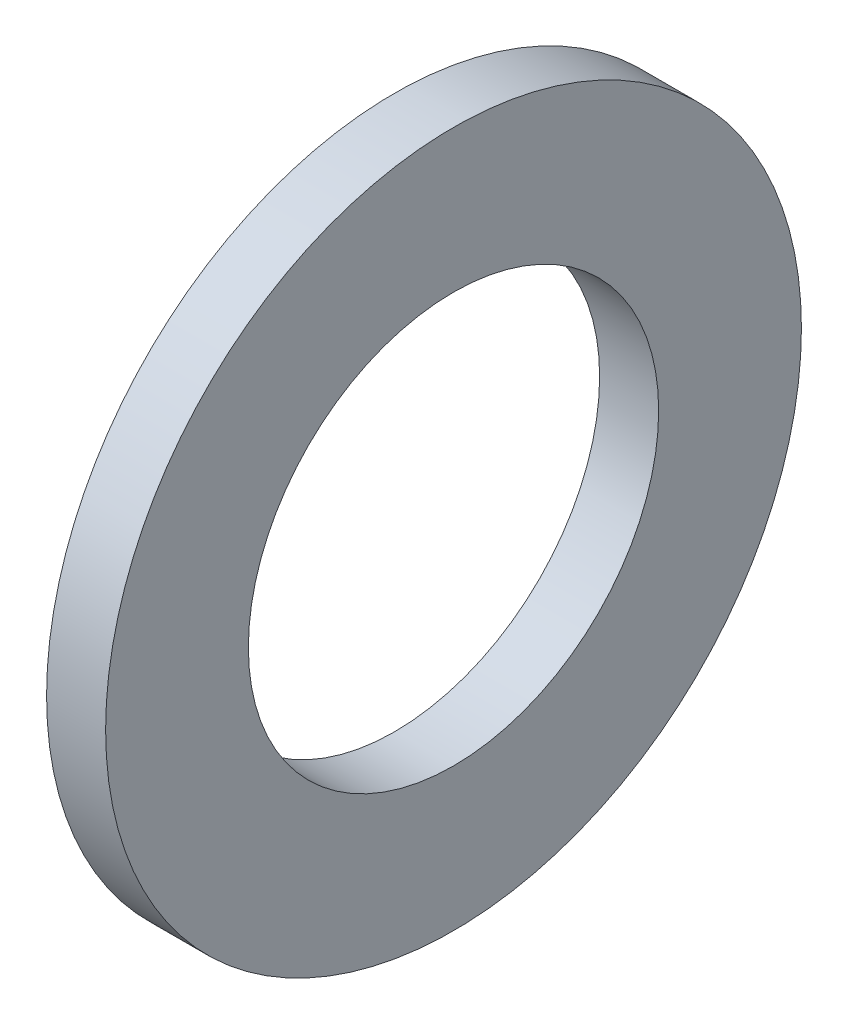
SolidWorks part; units mm, degrees
ref_plane "Plane1" through (0, 0, 0) normal (0, 0, 1) x (1, 0, 0)
ref_plane "Plane2" through (0, 0, 0) normal (0, 1, 0) x (1, 0, 0)
ref_plane "Plane3" through (0, 0, 0) normal (1, 0, 0) x (0, 0, -1)
sketch "Sketch1" plane through (0, 0, 0) normal (0, 0, 1) x (1, 0, 0)
  line L0 (-34.925, 0) -> (9.525, 0) construction
  line L1 (0, 19.46) -> (0, 33)
  line L2 (0, 33) -> (-5.6, 33)
  line L3 (-5.6, 33) -> (-5.6, 19.46)
  line L4 (-5.6, 19.46) -> (0, 19.46)
  dimension "Thickness" = 5.6
  dimension "Inside_dia" = 38.92
  dimension "Outside_dia" = 66
revolve "Base-Revolve" add sketch "Sketch1" angle 360 about L0
